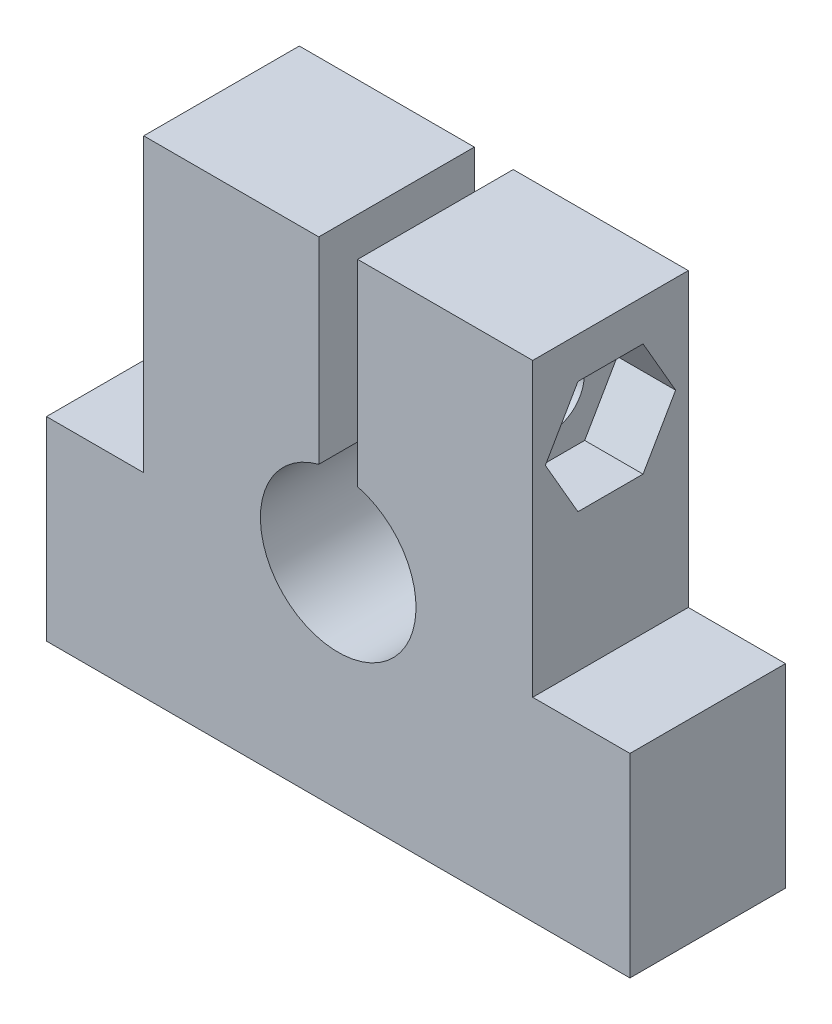
SolidWorks part; units mm, degrees
ref_plane "前视基准面" through (0, 0, 0) normal (0, 0, 1) x (1, 0, 0)
ref_plane "上视基准面" through (0, 0, 0) normal (0, 1, 0) x (1, 0, 0)
ref_plane "右视基准面" through (0, 0, 0) normal (1, 0, 0) x (0, 0, -1)
sketch "草图1" plane through (0, 0, 0) normal (0, 0, 1) x (1, 0, 0)
  line L0 (0, 0) -> (0, 30.4533) construction
  line L1 (-10, 25) -> (10, 25)
  line L2 (10, 25) -> (10, 10)
  line L3 (10, 10) -> (15, 10)
  line L4 (15, 10) -> (15, 0)
  line L5 (15, 0) -> (-15, 0)
  line L6 (-15, 10) -> (-15, 0)
  line L7 (-10, 10) -> (-15, 10)
  line L8 (-10, 25) -> (-10, 10)
  point P12 (0, 25)
  dimension "D1" = 20
  dimension "D2" = 30
  dimension "D3" = 10
  dimension "D4" = 25
extrude "凸台-拉伸1" add sketch "草图1" along normal blind 8
sketch "草图2" plane through (0, 0, 8) normal (0, 0, 1) x (1, 0, 0)
  line L0 (0, 0) -> (0, 41.462) construction
  line L1 (-15, 0) -> (15, 0) construction
  line L2 (-1, 25) -> (1, 25)
  line L3 (10, 25) -> (-10, 25) construction
  line L4 (1, 25) -> (1, 14.873)
  line L5 (-1, 25) -> (-1, 14.873)
  arc A0 (-1, 14.873) -> (1, 14.873) centre (0, 11) ccw
  point P14 (0, 25)
  dimension "D1" = 11
  dimension "D2" = 8
  dimension "D3" = 2
extrude "切除-拉伸1" cut sketch "草图2" against normal through all
sketch "草图3" plane through (-10, 0, 0) normal (-1, 0, 0) x (0, 0, 1)
  line L0 (4, 10) -> (4, 32.0252) construction
  line L1 (8, 10) -> (0, 10) construction
  line L2 (8, 0) -> (0, 0) construction
  circle A0 centre (4, 20) radius 1.65
  dimension "D1" = 3.3
  dimension "D2" = 20
extrude "切除-拉伸2" cut sketch "草图3" against normal through all
sketch "草图4" plane through (-10, 0, 0) normal (-1, 0, 0) x (0, 0, 1)
  circle A0 centre (4, 20) radius 3
  dimension "D1" = 6
extrude "切除-拉伸3" cut sketch "草图4" against normal blind 3.3
sketch "草图5" plane through (10, 0, 0) normal (1, 0, 0) x (0, 0, -1)
  line L1 (-7.3486, 20) -> (-5.6743, 17.1)
  line L2 (-5.6743, 17.1) -> (-2.3257, 17.1)
  line L3 (-2.3257, 17.1) -> (-0.6514, 20)
  line L4 (-0.6514, 20) -> (-2.3257, 22.9)
  line L5 (-2.3257, 22.9) -> (-5.6743, 22.9)
  line L6 (-5.6743, 22.9) -> (-7.3486, 20)
  circle A0 centre (-4, 20) radius 2.9 construction
  dimension "D1" = 5.8
extrude "切除-拉伸4" cut sketch "草图5" against normal blind 3
